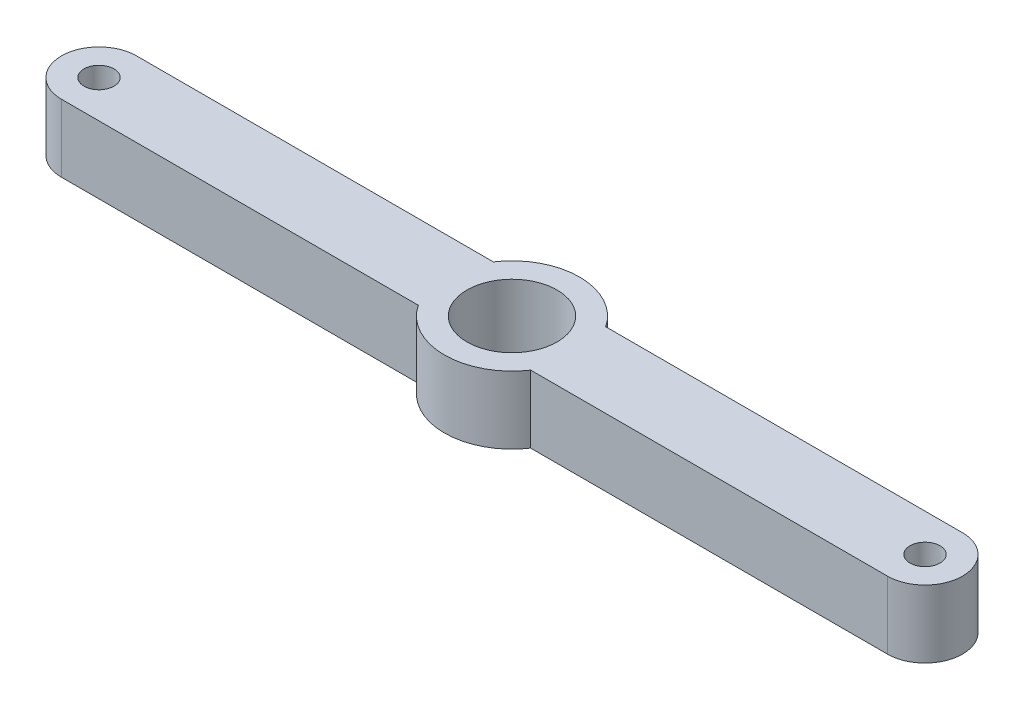
SolidWorks part; units mm, degrees
ref_plane "Front Plane" through (0, 0, 0) normal (0, 0, 1) x (1, 0, 0)
ref_plane "Top Plane" through (0, 0, 0) normal (0, 1, 0) x (1, 0, 0)
ref_plane "Right Plane" through (0, 0, 0) normal (1, 0, 0) x (0, 0, -1)
sketch "Sketch1" plane through (0, 0, 0) normal (0, 1, 0) x (1, 0, 0)
  line L0 (-3.7417, 2.5) -> (-27.5, 2.5)
  line L1 (27.5, -2.5) -> (3.7417, -2.5)
  line L3 (27.5, 2.5) -> (3.7417, 2.5)
  line L5 (27.5, -2.5) -> (-27.5, 2.5) construction
  line L6 (27.5, 2.5) -> (-27.5, -2.5) construction
  line L7 (-3.7417, -2.5) -> (-27.5, -2.5)
  arc A0 (-27.5, 2.5) -> (-27.5, -2.5) centre (-27.5, 0) ccw
  arc A1 (27.5, 2.5) -> (27.5, -2.5) centre (27.5, 0) cw
  arc A2 (-3.7417, -2.5) -> (3.7417, -2.5) centre (0, 0) ccw
  arc A3 (3.7417, 2.5) -> (-3.7417, 2.5) centre (0, 0) ccw
  point P0 (0, 0)
  dimension "D3" = 9
  dimension "D1" = 55
  dimension "D2" = 5
extrude "Boss-Extrude2" add sketch "Sketch1" along normal blind 4.5
sketch "Sketch2" plane through (0, 0, 0) normal (0, 1, 0) x (1, 0, 0)
  circle A0 centre (0, 0) radius 3
  dimension "D1" = 6
extrude "Cut-Extrude1" cut sketch "Sketch2" against normal through all both and the other way through all
sketch "Sketch3" plane through (0, 0, 0) normal (0, 1, 0) x (1, 0, 0)
  line L0 (0, 0) -> (0, 8.4133) construction
  circle A0 centre (-27.5, 0) radius 1
  circle A1 centre (27.5, 0) radius 1
  dimension "D1" = 2
  dimension "D2" = 55
extrude "Cut-Extrude2" cut sketch "Sketch3" against normal through all both and the other way through all
